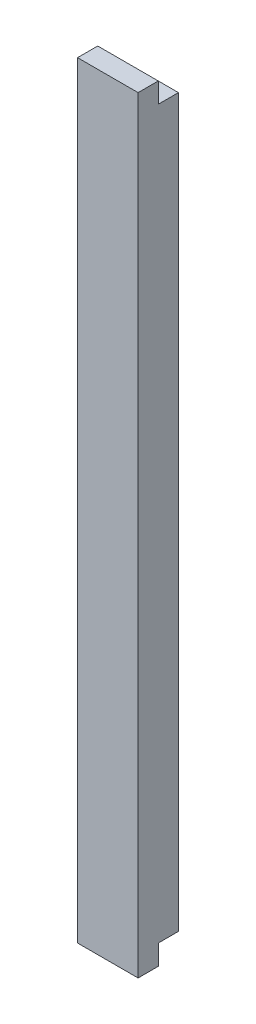
SolidWorks part; units mm, degrees
ref_plane "Front Plane" through (0, 0, 0) normal (0, 0, 1) x (1, 0, 0)
ref_plane "Top Plane" through (0, 0, 0) normal (0, 1, 0) x (1, 0, 0)
ref_plane "Right Plane" through (0, 0, 0) normal (1, 0, 0) x (0, 0, -1)
sketch "Sketch1" plane through (0, 0, 0) normal (0, 0, 1) x (1, 0, 0)
  line L0 (-20, 190) -> (20, 190)
  line L1 (20, 190) -> (20, -190)
  line L2 (20, -190) -> (-20, -190)
  line L3 (-20, -190) -> (-20, 190)
  point P2 (0, 190)
  point P5 (-20, 0)
  dimension "D1" = 40
  dimension "D2" = 380
extrude "Boss-Extrude1" add sketch "Sketch1" along normal blind 20
sketch "Sketch2" plane through (0, 0, 20) normal (0, 0, 1) x (1, 0, 0)
  line L1 (-10, 190) -> (-10, -190)
  line L4 (-20, 190) -> (-20, -190)
  line L5 (-20, -190) -> (20, -190)
  line L6 (20, -190) -> (20, 190)
  line L7 (20, 190) -> (-20, 190)
  line L8 (-20, 190) -> (-20, -190)
  line L9 (-20, -190) -> (-10, -190)
  line L11 (-10, 190) -> (-20, 190)
  line L12 (10, -180) -> (10, 180) construction
  line L13 (10, 180) -> (-10, 180) construction
  line L14 (-10, -180) -> (10, -180) construction
  line L16 (20, -190) -> (20, 190) construction
  line L17 (-10, 180) -> (-10, -180) construction
  line L18 (20, 190) -> (-20, 190) construction
  line L19 (-20, -190) -> (20, -190) construction
  point P8 (0, 0)
  dimension "D1" = 0
  dimension "D2" = 10
extrude "Cut-Extrude1" cut sketch "Sketch2" against normal blind 10
sketch "Sketch3" plane through (0, 0, 0) normal (0, 0, -1) x (-1, 0, 0)
  line L2 (-20, 180) -> (20, 180)
  line L3 (-20, 180) -> (20, 180)
  line L8 (-20, -180) -> (-20, -190)
  line L9 (20, -180) -> (-20, -180)
  line L10 (20, -180) -> (-20, -180)
  line L11 (20, 180) -> (20, 190)
  line L14 (20, -190) -> (20, 190)
  line L15 (20, 190) -> (-20, 190)
  line L16 (-20, 190) -> (-20, -190)
  line L17 (-20, -190) -> (20, -190)
  line L18 (20, -190) -> (20, -180)
  line L19 (20, 190) -> (-20, 190)
  line L20 (-20, 190) -> (-20, 180)
  line L21 (-20, -190) -> (20, -190)
  dimension "D1" = 10
  dimension "D2" = 10
  dimension "D3" = 0
extrude "Cut-Extrude2" cut sketch "Sketch3" against normal blind 10
